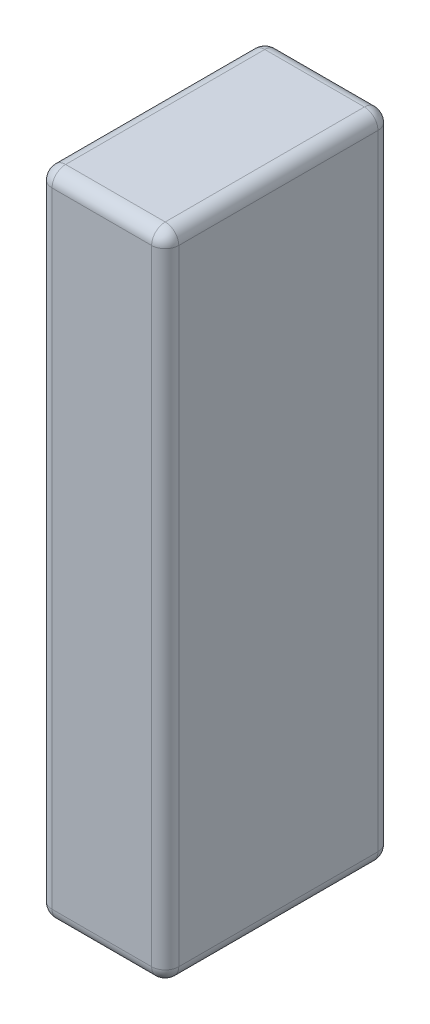
SolidWorks part; units mm, degrees
material "Lipo 3S"
ref_plane "Front Plane" through (0, 0, 0) normal (0, 0, 1) x (1, 0, 0)
ref_plane "Top Plane" through (0, 0, 0) normal (0, 1, 0) x (1, 0, 0)
ref_plane "Right Plane" through (0, 0, 0) normal (1, 0, 0) x (0, 0, -1)
sketch "Sketch1" plane through (0, 0, 0) normal (0, 1, 0) x (1, 0, 0)
  line L1 (0, 0) -> (28, 0)
  line L2 (0, 0) -> (0, 50)
  line L3 (0, 50) -> (28, 50)
  line L4 (28, 0) -> (28, 50)
  dimension "D1" = 50
  dimension "D2" = 28
extrude "Boss-Extrude1" add sketch "Sketch1" along normal blind 144
fillet "Fillet1" radius 3 12 edges at (14, 144, -50) (14, 0, -50) (0, 72, -50) (0, 144, -25) (0, 0, -25) (28, 144, -25) (28, 72, -50) (28, 0, -25) (0, 72, 0) (14, 144, 0) (28, 72, 0) (14, 0, 0)
